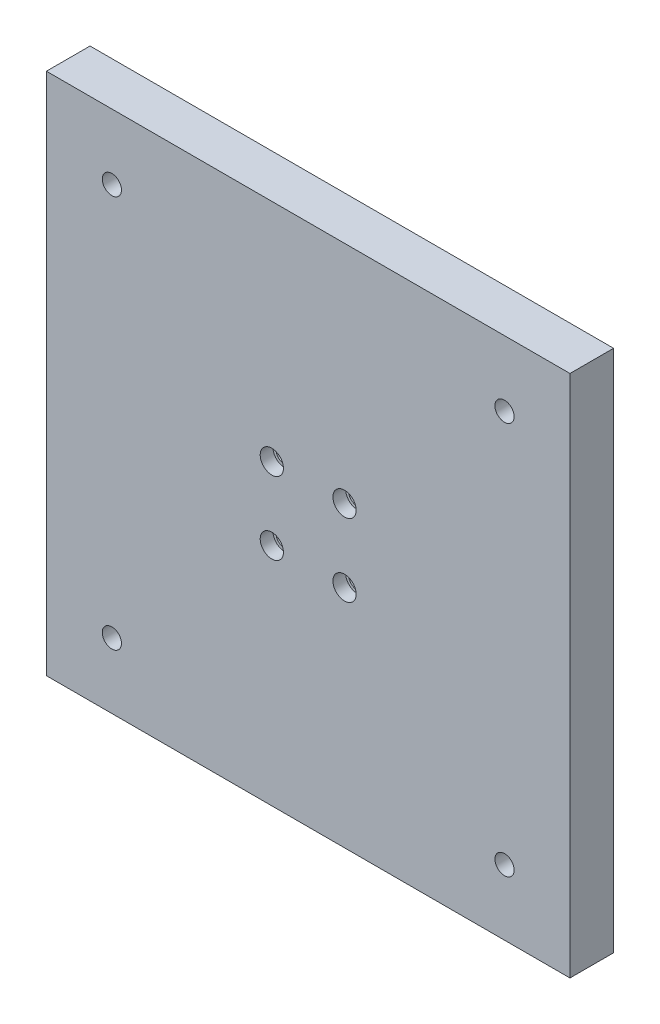
SolidWorks part; units mm, degrees
material "Verre"
ref_plane "Plan de face" through (0, 0, 0) normal (0, 0, 1) x (1, 0, 0)
ref_plane "Plan de dessus" through (0, 0, 0) normal (0, 1, 0) x (1, 0, 0)
ref_plane "Plan de droite" through (0, 0, 0) normal (1, 0, 0) x (0, 0, -1)
sketch "Esquisse1" plane through (0, 0, 0) normal (0, 0, 1) x (1, 0, 0)
  line L0 (-22.5, 157.5) -> (-22.5, 22.5) construction
  line L1 (0, 0) -> (-180, 0)
  line L2 (0, 0) -> (0, 180)
  line L3 (0, 180) -> (-180, 180)
  line L4 (-180, 0) -> (-180, 180)
  line L5 (-22.5, 22.5) -> (-157.5, 22.5) construction
  circle A0 centre (-22.5, 22.5) radius 3
  circle A1 centre (-157.5, 22.5) radius 3
  circle A2 centre (-157.5, 157.5) radius 3
  circle A3 centre (-22.5, 157.5) radius 3
  point P7 (-90, 22.5)
  point P9 (-90, 0)
  point P15 (-22.5, 90)
  point P16 (0, 90)
  dimension "D3" = 2
  dimension "D1" = 180
  dimension "D2" = 180
  dimension "D4" = 2
extrude "Boss.-Extru.1" add sketch "Esquisse1" along normal blind 15
sketch "Esquisse6" plane through (0, 0, 15) normal (0, 0, 1) x (1, 0, 0)
  line L0 (-102.5, 102.5) -> (-102.5, 77.5) construction
  line L1 (-102.5, 77.5) -> (-77.5, 77.5) construction
  line L2 (0, 180) -> (-180, 180) construction
  line L3 (-180, 180) -> (-180, 0) construction
  circle A0 centre (-102.5, 77.5) radius 3
  circle A1 centre (-77.5, 77.5) radius 3
  circle A2 centre (-77.5, 102.5) radius 3
  circle A3 centre (-102.5, 102.5) radius 3
  point P2 (-90, 77.5)
  point P11 (-90, 180)
  point P12 (-102.5, 90)
  point P15 (-180, 90)
  dimension "D1" = 2
  dimension "D3" = 25
  dimension "D4" = 25
  dimension "D2" = 2
extrude "Enlèv. mat.-Extru.1" cut sketch "Esquisse6" against normal through all
hole_wizard "Chambrage pour vis à tête hexagonale M41" positions "Esquisse10" profile "Esquisse9" counterbore size "M4" standard "ISO" end condition through all
sketch "Esquisse10" plane through (0, 0, 15) normal (0, 0, 1) x (1, 0, 0)
  point P0 (-102.5, 77.5)
  point P4 (-102.5, 102.5)
  point P7 (-77.5, 102.5)
  point P10 (-77.5, 77.5)
sketch "Esquisse9" plane through (-102.5, 77.5, 15) normal (1, 0, 0) x (0, -1, 0)
  line L0 (0, 0) -> (0, 15)
  line L1 (0, 15) -> (2.25, 15)
  line L3 (2.25, 15) -> (2.25, 4.4)
  line L4 (2.25, 4.4) -> (4, 4.4)
  line L5 (4, 4.4) -> (4, 0)
  line L7 (4, 0) -> (0, 0)
  line L11 (0, -6.35) -> (0, 107.95) construction
  dimension "Diamètre du perçage jusqu'au prochain" = 4.5
  dimension "Profondeur du perçage jusqu'au prochain" = 15
  dimension "Diamètre du chambrage" = 8
  dimension "Profondeur du chambrage" = 4.4
hole_wizard "Chambrage pour vis à tête hexagonale M62" positions "Esquisse12" profile "Esquisse11" counterbore size "M6" standard "ISO" end condition through all
sketch "Esquisse12" plane through (0, 0, 0) normal (0, 0, -1) x (-1, 0, 0)
  point P0 (157.5, 22.5)
  point P3 (22.5, 22.5)
  point P6 (22.5, 157.5)
  point P9 (157.5, 157.5)
sketch "Esquisse11" plane through (-157.5, 22.5, 0) normal (1, 0, 0) x (0, 1, 0)
  line L0 (0, 0) -> (0, 15)
  line L1 (0, 15) -> (3.3, 15)
  line L3 (3.3, 15) -> (3.3, 6.4)
  line L4 (3.3, 6.4) -> (5.5, 6.4)
  line L5 (5.5, 6.4) -> (5.5, 0)
  line L7 (5.5, 0) -> (0, 0)
  line L11 (0, -6.35) -> (0, 107.95) construction
  dimension "Diamètre du perçage jusqu'au prochain" = 6.6
  dimension "Profondeur du perçage jusqu'au prochain" = 15
  dimension "Diamètre du chambrage" = 11
  dimension "Profondeur du chambrage" = 6.4
